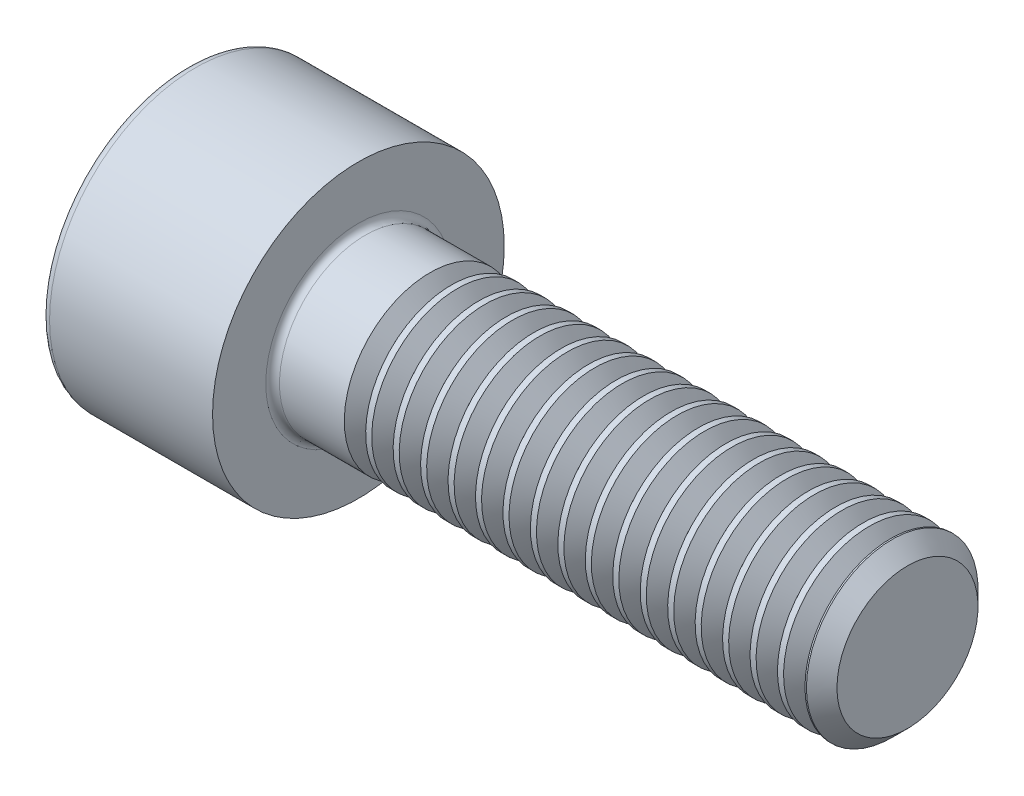
SolidWorks part; units mm, degrees
ref_plane "Plane1" through (0, 0, 0) normal (0, 0, 1) x (1, 0, 0)
ref_plane "Plane2" through (0, 0, 0) normal (0, 1, 0) x (1, 0, 0)
ref_plane "Plane3" through (0, 0, 0) normal (1, 0, 0) x (0, 0, -1)
sketch "BodySke" plane through (0, 0, 0) normal (0, 0, 1) x (1, 0, 0)
  line L0 (0, 0) -> (0, 4.25)
  line L1 (0, 4.25) -> (5, 4.25)
  line L2 (5, 4.25) -> (5, 2.5)
  line L3 (5, 2.5) -> (20.555, 2.5)
  line L4 (21, 2.055) -> (21, 0)
  line L5 (21, 0) -> (0, 0)
  line L6 (-31.75, 0) -> (127, 0) construction
  line L8 (21, 2.055) -> (20.555, 2.5)
  line L10 (21, -2.055) -> (20.555, -2.5) construction
  line L11 (5.8, 9.525) -> (5.8, 3.175) construction
  line L12 (5, 9.525) -> (5, 3.175) construction
  line L13 (-39, 9.525) -> (-39, 3.175) construction
  dimension "Diameter" = 5
  dimension "Head_ht" = 5
  dimension "Length" = 16
  dimension "Body_ch_ang" = 45
  dimension "Head_dia" = 8.5
  dimension "Minor_dia" = 4.11
  dimension "Advance" = 0.8
  dimension "Thread_nom" = 16
  dimension "Thread_length" = 60
revolve "Base-Revolve" add sketch "BodySke"
cosmetic thread "ThreadCosmetic" [suppressed]
fillet "Fillet1" radius 0.2 1 edges at (5, 0, 2.5)
fillet "Fillet2" radius 0.25 1 edges at (0, 0, 4.25)
sketch "Sketch2" plane through (0, 0, 0) normal (0, 0, 1) x (1, 0, 0)
  line L0 (0, 2.042) -> (2.5, 2.042)
  line L1 (2.5, 2.042) -> (3.6789, 0)
  line L2 (-31.75, 0) -> (127, 0) construction
  line L3 (3.6789, 0) -> (0, 0)
  line L4 (0, 0) -> (0, 2.042)
  line L6 (0, 0) -> (47.625, 0) construction
  dimension "D1" = 2.042
  dimension "D2" = 60
  dimension "Depth" = 2.5
revolve "Hex-PreBroach" cut sketch "Sketch2" angle 360 about L6
sketch "Sketch3" plane through (0, 0, 0) normal (-1, 0, 0) x (0, 0.5, 0.866)
  line L0 (1.1789, 2.042) -> (-1.1789, 2.042)
  line L1 (-1.1789, 2.042) -> (-2.3579, 0)
  line L2 (1.1789, 2.042) -> (2.3579, 0)
  line L3 (1.1789, -2.042) -> (2.3579, 0)
  line L4 (1.1789, -2.042) -> (-1.1789, -2.042)
  line L5 (-1.1789, -2.042) -> (-2.3579, 0)
  dimension "D1" = 2.042
  dimension "D2" = 2.042
  dimension "Hex_size" = 4.084
extrude "Hex" cut sketch "Sketch3" against normal blind 2.5
sketch "ThdSchSke" plane through (0, 0, 0) normal (0, 0, 1) x (1, 0, 0)
  line L0 (7.4, -2.055) -> (7.0884, -2.5)
  line L1 (7.4, -2.055) -> (7.7116, -2.5)
  line L2 (7.7116, -2.5) -> (7.7116, -3.125)
  line L3 (-3.175, 0) -> (5.1513, 0) construction
  line L4 (0, 4) -> (0, -4) construction
  line L5 (7.7116, -3.125) -> (7.0884, -3.125)
  line L6 (7.0884, -3.125) -> (7.0884, -2.5)
  dimension "Thread_minor" = 4.11
  dimension "Diameter" = 5
  dimension "Start" = 7.4
  dimension "SideAngle" = 55
  dimension "VeeAngle" = 70
  dimension "Overcut" = 6.25
revolve "ThreadSchematic" cut sketch "ThdSchSke" angle 360 about L3
pattern_linear "ThdSchPat" count 17 spacing 0.8 along (1, 0, 0) of "ThreadSchematic"
equation "\"D2@Sketch3\" = \"Hex_size@Sketch3\" / 2"
equation "\"D1@Sketch3\" = \"Hex_size@Sketch3\" / 2"
equation "\"D1@Sketch2\" = \"Hex_size@Sketch3\" / 2"
equation "\"Thread_minor@ThreadCosmetic\"  =  \"Minor_dia@BodySke\""
equation "\"Depth@Sketch2\" =  \"Key_eng@Hex\""
equation "\"Thread_length@ThreadCosmetic\" = ((sgn( (\"Length@BodySke\" - \"Advance@BodySke\" * 3.0) - \"Thread_nom@BodySke\" )-1)*( (\"Length@BodySke\" - \"Advance@BodySke\" * 3.0) - \"Thread_nom@BodySke\" ))/-2+ \"Thread_nom@BodySke\""
equation "\"Thread_minor@ThdSchSke\" = \"Minor_dia@BodySke\""
equation "\"Diameter@ThdSchSke\" = \"Diameter@BodySke\""
equation "\"Overcut@ThdSchSke\" = \"Diameter@BodySke\" * 1.25"
equation "\"Start@ThdSchSke\" = \"Head_ht@BodySke\" + \"Length@BodySke\" - \"Thread_length@ThreadCosmetic\"  '---Non-countersunk---"
equation "\"Num_threads@ThdSchPat\" = int( \"Thread_length@ThreadCosmetic\" / \"Advance@BodySke\" + 0.999 )  + 1"
equation "\"Advance@ThdSchPat\" = \"Thread_length@ThreadCosmetic\" /  (\"Num_threads@ThdSchPat\" - 1) 'relax it"
equation "\"Num_threads@ThdSchPat\" = \"Num_threads@ThdSchPat\" - sgn( \"Num_threads@ThdSchPat\" - 1) '---chamfered tips only---"
